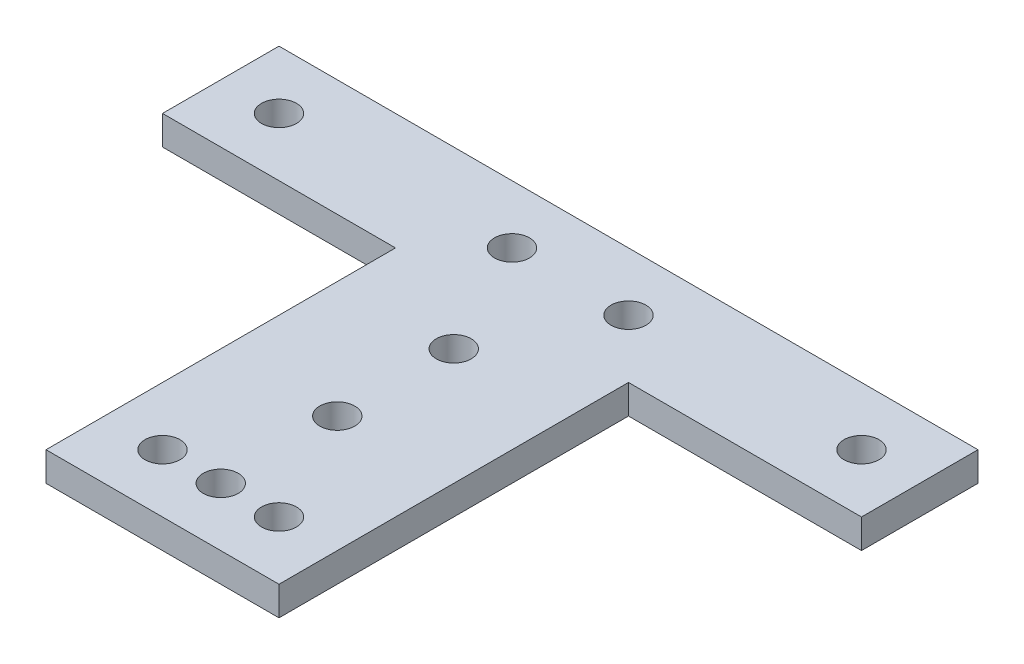
SolidWorks part; units mm, degrees
ref_plane "Plan de face" through (0, 0, 0) normal (0, 0, 1) x (1, 0, 0)
ref_plane "Plan de dessus" through (0, 0, 0) normal (0, 1, 0) x (1, 0, 0)
ref_plane "Plan de droite" through (0, 0, 0) normal (1, 0, 0) x (0, 0, -1)
sketch "Esquisse1" plane through (0, 0, 0) normal (0, 1, 0) x (1, 0, 0)
  line L0 (-30, -5) -> (-10, -5)
  line L1 (-30, 5) -> (30, 5)
  line L2 (-30, 5) -> (-30, -5)
  line L3 (-10, -5) -> (-10, -35)
  line L4 (30, 5) -> (30, -5)
  line L5 (-10, -35) -> (10, -35)
  line L6 (10, -35) -> (10, -5)
  line L7 (10, -5) -> (30, -5)
  circle A0 centre (-25, 0) radius 1.5
  circle A1 centre (25, 0) radius 1.5
  circle A2 centre (-5, 0) radius 1.5
  circle A3 centre (5, 0) radius 1.5
  circle A4 centre (-5, -30) radius 1.5
  circle A5 centre (5, -30) radius 1.5
  circle A6 centre (0, -30) radius 1.5
  circle A7 centre (0, -20) radius 1.5
  circle A9 centre (0, -10) radius 1.5
  dimension "D7" = 3
  dimension "D8" = 3
  dimension "D13" = 3
  dimension "D14" = 3
  dimension "D25" = 3
  dimension "D26" = 3
  dimension "D27" = 3
  dimension "D28" = 3
  dimension "D38" = 3
  dimension "D1" = 60
  dimension "D2" = 10
  dimension "D3" = 30
  dimension "D4" = 5
  dimension "D5" = 25
  dimension "D6" = 25
  dimension "D9" = 5
  dimension "D10" = 5
  dimension "D11" = 5
  dimension "D12" = 5
  dimension "D15" = 5
  dimension "D16" = 5
  dimension "D17" = 20
  dimension "D18" = 20
  dimension "D19" = 30
  dimension "D20" = 10
  dimension "D21" = 10
  dimension "D22" = 10
  dimension "D23" = 5
  dimension "D24" = 10
  dimension "D29" = 5
  dimension "D30" = 5
  dimension "D31" = 5
  dimension "D32" = 10
  dimension "D33" = 10
  dimension "D34" = 10
extrude "Boss.-Extru.1" add sketch "Esquisse1" along normal blind 2.5
